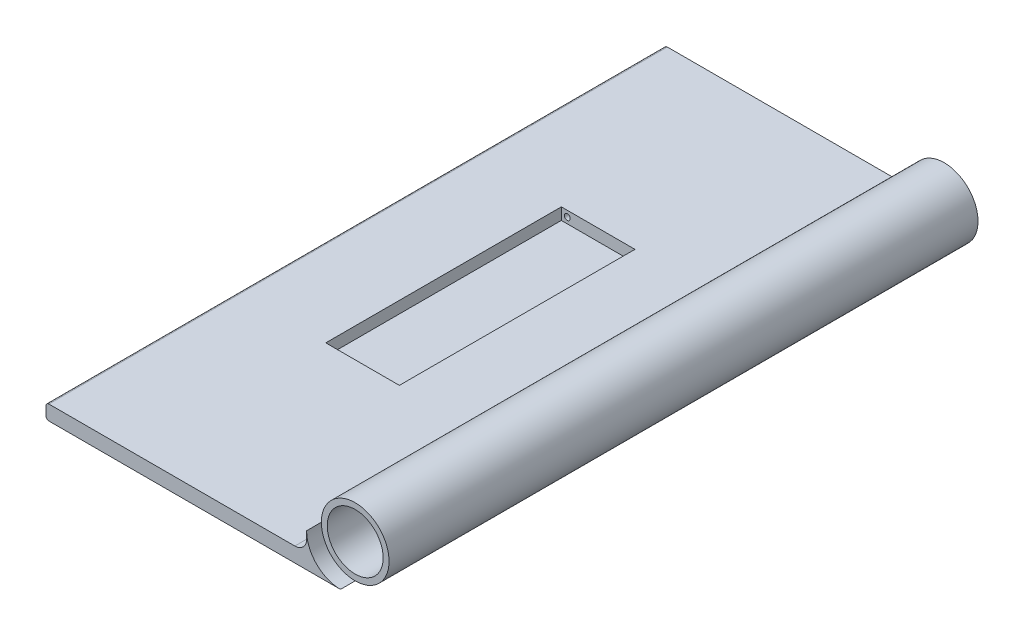
SolidWorks part; units mm, degrees
ref_plane "Front" through (0, 0, 0) normal (0, 0, 1) x (1, 0, 0)
ref_plane "Top" through (0, 0, 0) normal (0, 1, 0) x (1, 0, 0)
ref_plane "Right" through (0, 0, 0) normal (1, 0, 0) x (0, 0, -1)
sketch "草图1" plane through (0, 0, 0) normal (0, 0, 1) x (1, 0, 0)
  line L0 (-11.5, 0) -> (-11.5, -2.5)
  line L1 (0, -11.5) -> (-99, -11.5)
  line L3 (-15.5, -6.5) -> (-99, -6.5)
  line L4 (-100, -10.5) -> (-100, -7.5)
  circle A0 centre (0, 0) radius 9.5
  circle A1 centre (0, 0) radius 11.5
  arc A2 (-15.5, -6.5) -> (-11.5, -2.5) centre (-15.5, -2.5) ccw
  arc A3 (-99, -11.5) -> (-100, -10.5) centre (-99, -10.5) cw
  arc A4 (-99, -6.5) -> (-100, -7.5) centre (-99, -7.5) ccw
  point P13 (-100, -11.5)
  point P16 (-100, -6.5)
  dimension "D1" = 23
  dimension "D2" = 19
  dimension "D5" = 4
  dimension "D6" = 1
  dimension "D3" = 100
  dimension "D4" = 5
extrude "凸台-拉伸1" add sketch "草图1" along normal blind 200 contours L3 A4 L4 A3 L1 A1 L0 A2 | A1 A0
sketch "草图2" plane through (0, 0, 0) normal (0, 0, -1) x (-1, 0, 0)
  line L0 (11.5, 0) -> (11.5, -2.5)
  line L1 (0, -11.5) -> (99, -11.5)
  line L3 (15.5, -6.5) -> (99, -6.5)
  line L4 (100, -10.5) -> (100, -7.5)
  circle A0 centre (0, 0) radius 11.5
  arc A1 (11.5, -2.5) -> (15.5, -6.5) centre (15.5, -2.5) ccw
  arc A2 (99, -11.5) -> (100, -10.5) centre (99, -10.5) ccw
  arc A3 (99, -6.5) -> (100, -7.5) centre (99, -7.5) cw
  line M1 (99, -6.5) -> (15.5, -6.5)
  arc M2 (15.5, -6.5) -> (11.5, -2.5) centre (15.5, -2.5) cw
  line M3 (11.5, -2.5) -> (11.5, 0)
  line M5 (0, -11.5) -> (99, -11.5)
  arc M6 (99, -11.5) -> (100, -10.5) centre (99, -10.5) ccw
  line M7 (100, -10.5) -> (100, -7.5)
  arc M8 (100, -7.5) -> (99, -6.5) centre (99, -7.5) ccw
  dimension "D1" = 4
  dimension "D2" = 1
extrude "凸台-拉伸2" add sketch "草图2" along normal blind 5 and the other way blind 205 contours A0 M5 M6 M7 M8 M1 M2 M3
sketch "草图3" plane through (0, -6.5, 0) normal (0, 1, 0) x (1, 0, 0)
  line L1 (-70, -60) -> (-45, -60)
  line L2 (-70, -60) -> (-70, -140)
  line L3 (-70, -140) -> (-45, -140)
  line L4 (-45, -60) -> (-45, -140)
  dimension "D1" = 60
  dimension "D2" = 80
  dimension "D3" = 25
  dimension "D4" = 70
extrude "切除-拉伸1" cut sketch "草图3" against normal blind 4
sketch "草图4" plane through (0, 0, 60) normal (0, 0, 1) x (1, 0, 0)
  line L0 (-70, -10.5) -> (-70, -6.5) construction
  line L1 (-45, -6.5) -> (-70, -6.5) construction
  circle A0 centre (-68, -8.5) radius 1
  dimension "D1" = 2
  dimension "D2" = 2
  dimension "D3" = 2
extrude "切除-拉伸2" cut sketch "草图4" against normal blind 4 and the other way blind 81
